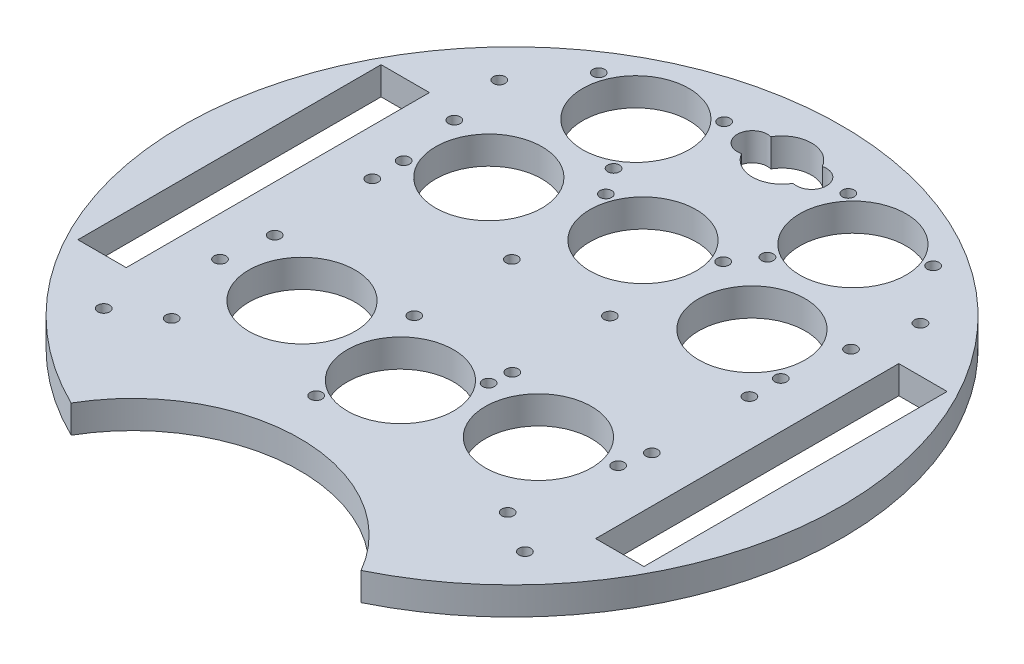
SolidWorks part; units mm, degrees
ref_plane "Front Plane" through (0, 0, 0) normal (0, 0, 1) x (1, 0, 0)
ref_plane "Top Plane" through (0, 0, 0) normal (0, 1, 0) x (1, 0, 0)
ref_plane "Right Plane" through (0, 0, 0) normal (1, 0, 0) x (0, 0, -1)
sketch "Sketch1" plane through (0, 0, 0) normal (0, 1, 0) x (1, 0, 0)
  line L1 (0, 86.2583) -> (0, -96.8543) construction
  line L3 (-32.9956, -67.352) -> (0, -86.402) construction
  line L4 (32.9956, -67.352) -> (0, -86.402) construction
  line L5 (0, 0) -> (-13.6167, -50.8184) construction
  line L6 (55.5325, -36.9707) -> (45.152, -29.4289) construction
  line L7 (0, 0) -> (-48.2091, 57.4533) construction
  line L8 (-83.3992, 0) -> (107.0959, 0) construction
  line L9 (53.4101, -34.3971) -> (53.4101, 34.6029)
  line L10 (-64.4101, -34.3971) -> (-53.4101, -34.3971)
  line L11 (-64.4101, -34.3971) -> (-64.4101, 34.6029)
  line L12 (-64.4101, 34.6029) -> (-53.4101, 34.6029)
  line L13 (-53.4101, -34.3971) -> (-53.4101, 34.6029)
  line L14 (64.4101, 34.6029) -> (53.4101, 34.6029)
  line L15 (64.4101, -34.3971) -> (64.4101, 34.6029)
  line L16 (64.4101, -34.3971) -> (53.4101, -34.3971)
  line L17 (0, 0) -> (13.6167, -50.8184) construction
  line L18 (41.9192, -33.8784) -> (45.152, -29.4289) construction
  line L19 (0, 0) -> (48.2091, 57.4533) construction
  line L20 (52.2843, -41.4268) -> (41.9192, -33.8784) construction
  line L21 (64.9519, -37.5) -> (0, 0) construction
  line L22 (28.5723, -45.8735) -> (34.7503, -57.019) construction
  line L23 (28.5723, -45.8735) -> (23.7619, -48.54) construction
  line L24 (44.9916, 49.3407) -> (36.7843, 39.5596) construction
  line L25 (32.5711, 43.0949) -> (36.7843, 39.5596) construction
  line L26 (23.7619, -48.54) -> (29.9399, -59.6854) construction
  line L27 (-28.5723, -45.8735) -> (-34.7503, -57.019) construction
  line L28 (-23.7619, -48.54) -> (-29.9399, -59.6854) construction
  line L29 (-18.4555, -45.8919) -> (-23.0541, -33.9225) construction
  line L30 (-23.0541, -33.9225) -> (-17.92, -31.9499) construction
  line L31 (-28.5723, -45.8735) -> (-23.7619, -48.54) construction
  line L32 (-40.7784, 52.876) -> (-32.5711, 43.0949) construction
  line L33 (-32.5711, 43.0949) -> (-36.7843, 39.5596) construction
  line L34 (40.7784, 52.876) -> (32.5711, 43.0949) construction
  line L35 (-13.6167, -50.8184) -> (-25.1096, -20.9046) construction
  line L36 (-44.9916, 49.3407) -> (-36.7843, 39.5596) construction
  line L37 (-13.3214, -43.9193) -> (-17.92, -31.9499) construction
  line L38 (13.6167, -50.8184) -> (24.3327, -22.8079) construction
  line L39 (18.4555, -45.8919) -> (23.0541, -33.9225) construction
  line L40 (23.0541, -33.9225) -> (17.92, -31.9499) construction
  line L41 (13.3214, -43.9193) -> (17.92, -31.9499) construction
  line L42 (-58.5537, 0) -> (91.2411, 0) construction
  line L43 (-55.5325, -36.9707) -> (-45.152, -29.4289) construction
  line L44 (-52.2843, -41.4268) -> (-41.9192, -33.8784) construction
  line L45 (-41.9192, -33.8784) -> (-45.152, -29.4289) construction
  line L46 (0, 34.6626) -> (0, -51.647) construction
  line L47 (-37.1849, 0) -> (48.113, 0) construction
  line L48 (0, 49.2959) -> (0, -33.0158) construction
  line L54 (8.45, 45.0502) -> (-8.45, 71.1502) construction
  line L55 (8.45, 71.1502) -> (-8.45, 45.0502) construction
  arc A0 (32.9956, -67.352) -> (-32.9956, -67.352) centre (0, 0) ccw
  arc A1 (32.9956, -67.352) -> (-32.9956, -67.352) centre (0, -86.402) ccw
  circle A2 centre (0, 0) radius 74 construction
  arc A3 (56.3744, 49.4664) -> (44.9543, 49.2959) centre (50.737, 44.5198) ccw construction
  arc A4 (-56.3744, 49.4664) -> (-44.9543, 49.2959) centre (-50.737, 44.5198) cw construction
  arc A5 (-45.9, -59.3143) -> (-34.7503, -57.019) centre (-41.31, -53.3829) ccw construction
  arc A6 (45.9, -59.3143) -> (34.7503, -57.019) centre (41.31, -53.3829) cw construction
  arc A7 (-38.9256, 64.1077) -> (-40.7407, 52.8315) centre (-35.033, 57.6969) ccw construction
  arc A8 (-25.9781, -70.3572) -> (-29.9399, -59.6854) centre (-23.3803, -63.3215) cw construction
  arc A9 (25.9781, -70.3572) -> (29.9399, -59.6854) centre (23.3803, -63.3215) ccw construction
  arc A10 (38.9256, 64.1077) -> (40.7407, 52.8315) centre (35.033, 57.6969) cw construction
  arc A11 (53.2525, -52.8127) -> (52.2843, -41.4268) centre (47.9272, -47.5314) ccw construction
  arc A12 (66.658, -34.376) -> (55.5325, -36.9707) centre (59.9914, -30.9401) cw construction
  arc A13 (-5.2684, -48.6449) -> (-13.3214, -43.9193) centre (-6.3241, -41.2196) cw construction
  arc A14 (-21.2728, -54.7938) -> (-18.4555, -45.8919) centre (-25.4604, -48.5717) ccw construction
  arc A15 (-66.658, -34.376) -> (-55.5325, -36.9707) centre (-59.9914, -30.9401) ccw construction
  arc A16 (-53.2525, -52.8127) -> (-52.2843, -41.4268) centre (-47.9272, -47.5314) cw construction
  arc A17 (21.2728, -54.7938) -> (18.4555, -45.8919) centre (25.4604, -48.5717) cw construction
  arc A18 (5.2684, -48.6449) -> (13.3214, -43.9193) centre (6.3241, -41.2196) ccw construction
  circle A19 centre (-42.9101, 11.1) radius 1.35
  circle A20 centre (-42.9101, -11.1) radius 1.35
  circle A21 centre (-11.1601, -11.1) radius 1.35
  circle A22 centre (-11.1601, 11.1) radius 1.35
  circle A23 centre (11.1601, 11.1) radius 1.35
  circle A24 centre (11.1601, -11.1) radius 1.35
  circle A25 centre (42.9101, -11.1) radius 1.35
  circle A26 centre (42.9101, 11.1) radius 1.35
  circle A27 centre (26.9058, -20.9046) radius 12.095
  circle A28 centre (24.6998, 52.876) radius 12.095
  circle A29 centre (0, 29.7936) radius 12.095
  circle A30 centre (0, -25.4092) radius 12.095
  circle A31 centre (29.9399, 24.6519) radius 12.095
  circle A32 centre (-26.9058, -20.9046) radius 12.095
  circle A33 centre (6.731, 61.4226) radius 1.143
  circle A34 centre (-6.731, 61.4226) radius 1.143
  arc A35 (-5.8539, 64.7449) -> (5.8576, 64.7385) centre (0, 61.4226) cw
  arc A36 (5.8576, 64.7385) -> (5.8576, 58.1067) centre (6.731, 61.4226) cw
  arc A37 (-5.8539, 58.1002) -> (-5.8539, 64.7449) centre (-6.731, 61.4226) cw
  arc A38 (5.8576, 58.1067) -> (-5.8539, 58.1002) centre (0, 61.4226) cw
  circle A39 centre (-29.9399, 24.6519) radius 12.095
  circle A40 centre (17.5039, 40.6135) radius 1.35
  circle A41 centre (14.1365, 62.3927) radius 1.35
  circle A42 centre (38.0467, 57.7763) radius 1.35
  circle A43 centre (-31.7919, 27.0969) radius 12.095 construction
  circle A44 centre (-42.9101, 18.2348) radius 1.35
  circle A45 centre (42.9101, 18.2348) radius 1.35
  circle A46 centre (-31.0383, -26.9744) radius 12.095 construction
  circle A47 centre (31.0383, -26.9744) radius 12.095 construction
  circle A48 centre (31.7919, 27.0969) radius 12.095 construction
  circle A49 centre (-24.6998, 52.876) radius 12.095
  circle A50 centre (45.1387, 31.9972) radius 1.35
  circle A51 centre (-45.1387, 31.9972) radius 1.35
  circle A52 centre (13.3469, 34.6938) radius 1.35
  circle A53 centre (-6.5548, -38.0261) radius 1.35
  circle A54 centre (-31.7919, 27.0969) radius 14.218 construction
  circle A55 centre (-13.3469, 34.6938) radius 1.35
  circle A56 centre (10.597, -15.93) radius 1.35
  circle A57 centre (-38.2343, -39.237) radius 1.35
  circle A58 centre (0, 29.7936) radius 14.218 construction
  circle A59 centre (-47.9272, -45.012) radius 1.35
  circle A60 centre (-47.9272, 45.012) radius 1.35
  circle A61 centre (47.9272, -45.012) radius 1.35
  circle A62 centre (31.7919, 27.0969) radius 14.218 construction
  circle A63 centre (-38.0467, 57.7763) radius 1.35
  circle A64 centre (-14.1365, 62.3927) radius 1.35
  circle A65 centre (-17.5039, 40.6135) radius 1.35
  circle A66 centre (-24.6998, 52.876) radius 14.218 construction
  circle A67 centre (47.9272, 45.012) radius 1.35
  circle A70 centre (24.6998, 52.876) radius 14.218 construction
  circle A71 centre (-44.3852, -22.0742) radius 1.35
  circle A74 centre (-31.0383, -26.9744) radius 14.218 construction
  circle A78 centre (0, -25.4092) radius 14.218 construction
  circle A80 centre (41.6017, -17.4578) radius 1.35
  circle A81 centre (38.2343, -39.237) radius 1.35
  circle A82 centre (31.0383, -26.9744) radius 14.218 construction
  point P14 (-62.6039, 0)
  point P23 (62.6039, 0)
  point P35 (-31.5178, -45.012)
  point P40 (-46.7211, -26.9744)
  point P45 (-34.6777, 41.3272)
  point P84 (-20.4871, -32.9362)
  point P154 (0, 58.1002)
  dimension "D1" = 150
  dimension "D2" = 76.2
  dimension "D10" = 148
  dimension "D13" = 2.7
  dimension "D14" = 2.7
  dimension "D22" = 2.286
  dimension "D20" = 2.7
  dimension "D3" = 120
  dimension "D4" = 69
  dimension "D5" = 11
  dimension "D9" = 30
  dimension "D16" = 5.5
  dimension "D7" = 5.5
  dimension "D8" = 12.8224
  dimension "D6" = 12.8224
  dimension "D11" = 5.5
  dimension "D12" = 5.5
  dimension "D17" = 22.2
  dimension "D19" = 22.2
  dimension "D15" = 10.5
  dimension "D18" = 31.75
  dimension "D23" = 13.462
  dimension "D24" = 16.9
  dimension "D25" = 26.1
extrude "Boss-Extrude2" add sketch "Sketch1" along normal blind 6.35 contours A1 A0 A81 A80 A71 A67 A65 A64 A63 A60 A59 A52 A51 A49 A42 A40 A36 A38 A37 A35 A32 A31 A30 A29 A28 A27 A24 A23
equation "\"D10@Sketch1\"=150-2"
